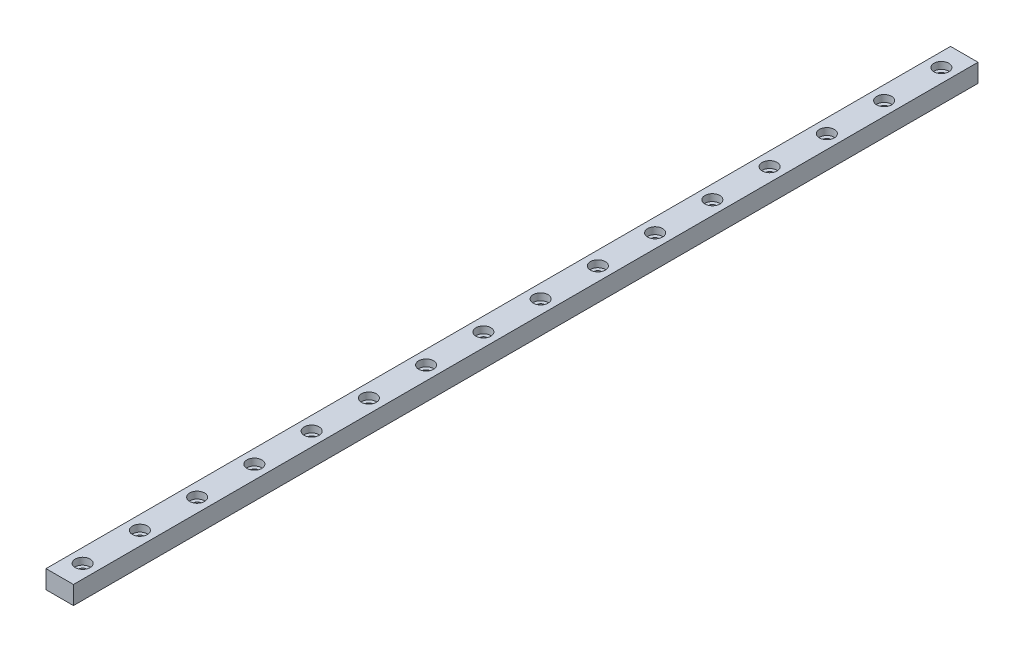
SolidWorks part; units mm, degrees
ref_plane "Front" through (0, 0, 0) normal (0, 0, 1) x (1, 0, 0)
ref_plane "Top" through (0, 0, 0) normal (0, 1, 0) x (1, 0, 0)
ref_plane "Right" through (0, 0, 0) normal (1, 0, 0) x (0, 0, -1)
sketch "Sketch1" plane through (0, 0, 0) normal (0, 0, 1) x (1, 0, 0)
  line L1 (0, 0) -> (12, 0)
  line L2 (0, 0) -> (0, 8)
  line L3 (0, 8) -> (12, 8)
  line L4 (12, 0) -> (12, 8)
  dimension "D1" = 12
  dimension "D2" = 8
extrude "Boss-Extrude1" add sketch "Sketch1" along normal blind 395
hole_wizard "CBORE for M3 SHCS1" positions "Sketch2" profile "Sketch3" counterbore size "M3" standard "ANSI Metric" end condition through all
sketch "Sketch2" plane through (0, 8, 0) normal (0, 1, 0) x (1, 0, 0)
  line L0 (12, -395) -> (0, -395) construction
  point P0 (6, -385)
  point P11 (6, -360)
  point P12 (6, -335)
  point P13 (6, -310)
  point P14 (6, -285)
  point P15 (6, -260)
  point P16 (6, -235)
  point P17 (6, -210)
  point P18 (6, -185)
  point P19 (6, -160)
  point P20 (6, -135)
  point P21 (6, -110)
  point P22 (6, -85)
  point P23 (6, -60)
  point P24 (6, -35)
  point P25 (6, -10)
  dimension "D1" = 10
  dimension "D2" = 16
sketch "Sketch3" plane through (6, 8, 385) normal (1, 0, 0) x (0, 0, 1)
  line L0 (0, 0) -> (0, 8)
  line L1 (0, 8) -> (1.7, 8)
  line L3 (1.7, 8) -> (1.7, 3)
  line L4 (1.7, 3) -> (3.25, 3)
  line L5 (3.25, 3) -> (3.25, 0)
  line L7 (3.25, 0) -> (0, 0)
  line L11 (0, -6.35) -> (0, 107.95) construction
  dimension "Thru Hole Dia." = 3.4
  dimension "Thru Hole Depth" = 8
  dimension "C'Bore Dia." = 6.5
  dimension "C'Bore Depth" = 3
equation "\"length\"=395"
equation "\"D1@Boss-Extrude1\"= \"length\""
